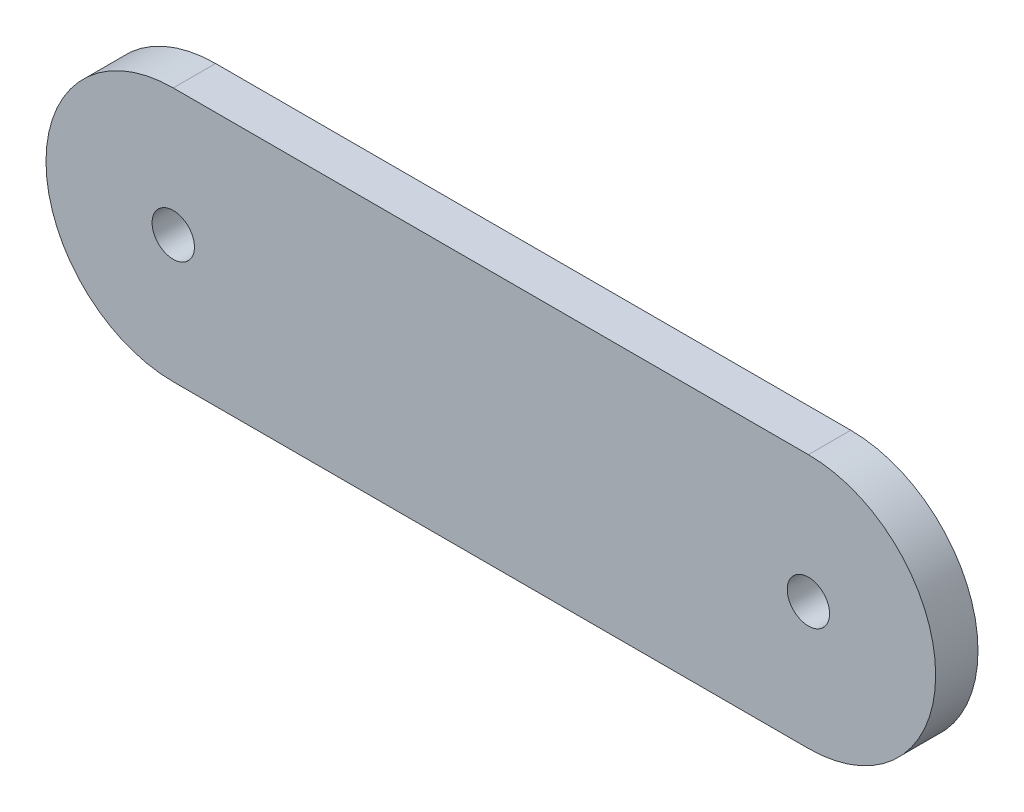
SolidWorks part; units mm, degrees
ref_plane "Front Plane" through (0, 0, 0) normal (0, 0, 1) x (1, 0, 0)
ref_plane "Top Plane" through (0, 0, 0) normal (0, 1, 0) x (1, 0, 0)
ref_plane "Right Plane" through (0, 0, 0) normal (1, 0, 0) x (0, 0, -1)
sketch "Sketch1" plane through (0, 0, 0) normal (0, 0, 1) x (1, 0, 0)
  line L1 (-15, 0) -> (15, 0) construction
  line L2 (-15, 6.0098) -> (15, 6.0098)
  line L3 (-15, -6.0098) -> (15, -6.0098)
  circle A4 centre (-15, 0) radius 1
  arc A6 (-15, 6.0098) -> (-15, -6.0098) centre (-15, 0) ccw
  arc A7 (15, -6.0098) -> (15, 6.0098) centre (15, 0) ccw
  circle A8 centre (15, 0) radius 1
  point P0 (15, 0)
  point P2 (0, 0)
  point P9 (0, 0)
  dimension "D2" = 2
  dimension "D5" = 2
  dimension "D6" = 6.0098
  dimension "D4" = 30
extrude "Boss-Extrude1" add sketch "Sketch1" along normal blind 2
